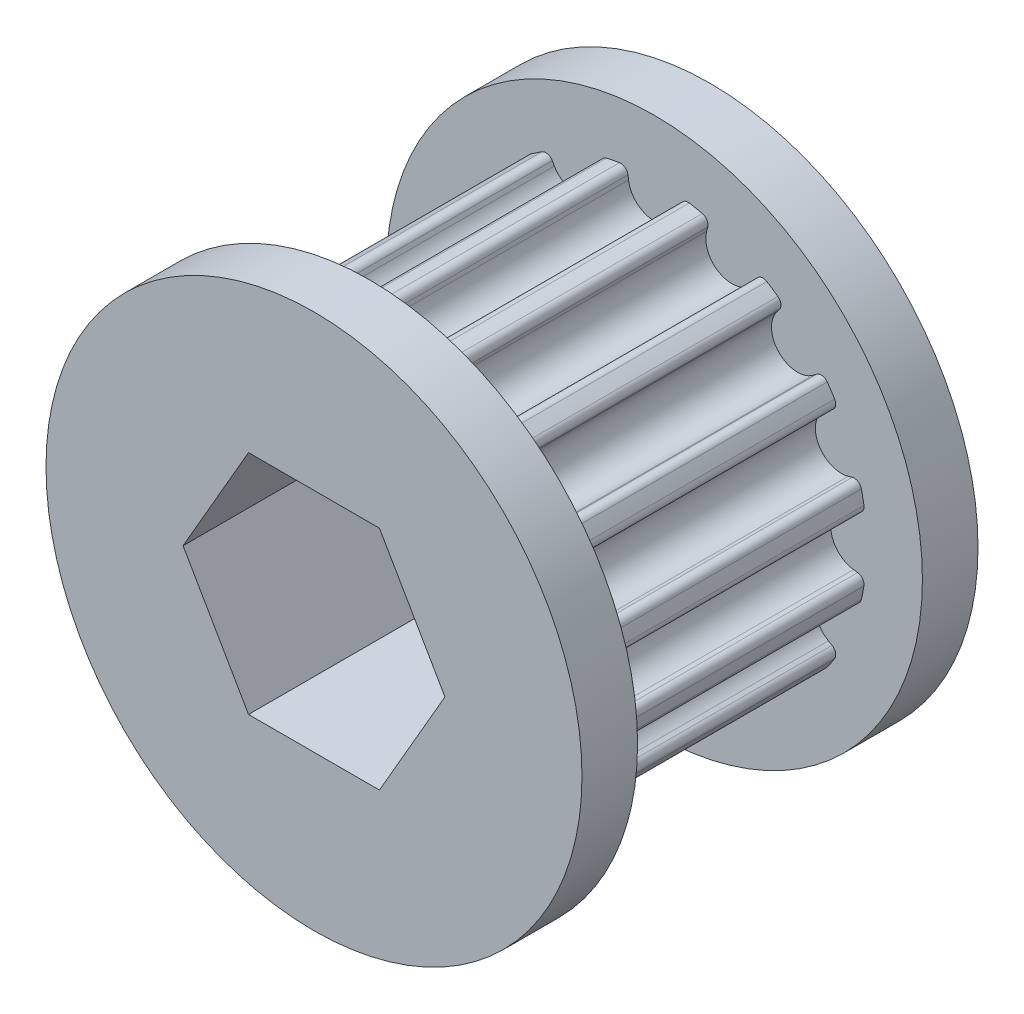
SolidWorks part; units mm, degrees
ref_plane "Front Plane" through (0, 0, 0) normal (0, 0, 1) x (1, 0, 0)
ref_plane "Top Plane" through (0, 0, 0) normal (0, 1, 0) x (1, 0, 0)
ref_plane "Right Plane" through (0, 0, 0) normal (1, 0, 0) x (0, 0, -1)
ref_plane "Plane1" through (0, 0, 0) normal (0, -1, 0) x (1, 0, 0)
sketch "Sketch1" plane through (0, 0, 0) normal (0, -1, 0) x (1, 0, 0)
  line L0 (15.3074, 3.175) -> (0, 3.175)
  line L1 (0, 3.175) -> (0, 0)
  line L2 (0, 0) -> (15.3074, 0)
  line L3 (15.3074, 0) -> (15.3074, 3.175)
  line L4 (0, 3.175) -> (0, 0) construction
revolve "Revolve1" add sketch "Sketch1" angle 360 about L4
sketch "Sketch2" plane through (0, 0, 3.175) normal (0, 0, 1) x (1, 0, 0)
  line L0 (1.5635, -12.0312) -> (1.4776, -11.3704)
  line L1 (-1.4776, -11.3704) -> (-1.5635, -12.0312)
  line L2 (-3.1597, -11.7137) -> (-2.9862, -11.0703)
  line L3 (-5.7164, -9.9394) -> (-6.0486, -10.5171)
  line L4 (-7.4018, -9.6129) -> (-6.9953, -9.0849)
  line L5 (-9.0849, -6.9953) -> (-9.6129, -7.4018)
  line L6 (-10.5171, -6.0486) -> (-9.9394, -5.7164)
  line L7 (-11.0703, -2.9862) -> (-11.7137, -3.1597)
  line L8 (-12.0312, -1.5635) -> (-11.3704, -1.4776)
  line L9 (-11.3704, 1.4776) -> (-12.0312, 1.5635)
  line L10 (-11.7137, 3.1597) -> (-11.0703, 2.9862)
  line L11 (-9.9394, 5.7164) -> (-10.5171, 6.0486)
  line L12 (-9.6129, 7.4018) -> (-9.0849, 6.9953)
  line L13 (-6.9953, 9.0849) -> (-7.4018, 9.6129)
  line L14 (-6.0486, 10.5171) -> (-5.7164, 9.9394)
  line L15 (-2.9862, 11.0703) -> (-3.1597, 11.7137)
  line L16 (-1.5635, 12.0312) -> (-1.4776, 11.3704)
  line L17 (1.4776, 11.3704) -> (1.5635, 12.0312)
  line L18 (3.1597, 11.7137) -> (2.9862, 11.0703)
  line L19 (5.7164, 9.9394) -> (6.0486, 10.5171)
  line L20 (7.4018, 9.6129) -> (6.9953, 9.0849)
  line L21 (9.0849, 6.9953) -> (9.6129, 7.4018)
  line L22 (10.5171, 6.0486) -> (9.9394, 5.7164)
  line L23 (11.0703, 2.9862) -> (11.7137, 3.1597)
  line L24 (12.0312, 1.5635) -> (11.3704, 1.4776)
  line L25 (11.3704, -1.4776) -> (12.0312, -1.5635)
  line L26 (11.7137, -3.1597) -> (11.0703, -2.9862)
  line L27 (9.9394, -5.7164) -> (10.5171, -6.0486)
  line L28 (9.6129, -7.4018) -> (9.0849, -6.9953)
  line L29 (6.9953, -9.0849) -> (7.4018, -9.6129)
  line L30 (6.0486, -10.5171) -> (5.7164, -9.9394)
  line L31 (2.9862, -11.0703) -> (3.1597, -11.7137)
  arc A0 (1.4776, -11.3704) -> (-1.4776, -11.3704) centre (0, -11.5624) ccw
  arc A1 (-1.5635, -12.0312) -> (-3.1597, -11.7137) centre (0, 0) cw
  arc A2 (-2.9862, -11.0703) -> (-5.7164, -9.9394) centre (-4.4247, -10.6823) ccw
  arc A3 (-6.0486, -10.5171) -> (-7.4018, -9.6129) centre (0, 0) cw
  arc A4 (-6.9953, -9.0849) -> (-9.0849, -6.9953) centre (-8.1758, -8.1758) ccw
  arc A5 (-9.6129, -7.4018) -> (-10.5171, -6.0486) centre (0, 0) cw
  arc A6 (-9.9394, -5.7164) -> (-11.0703, -2.9862) centre (-10.6823, -4.4247) ccw
  arc A7 (-11.7137, -3.1597) -> (-12.0312, -1.5635) centre (0, 0) cw
  arc A8 (-11.3704, -1.4776) -> (-11.3704, 1.4776) centre (-11.5624, 0) ccw
  arc A9 (-12.0312, 1.5635) -> (-11.7137, 3.1597) centre (0, 0) cw
  arc A10 (-11.0703, 2.9862) -> (-9.9394, 5.7164) centre (-10.6823, 4.4247) ccw
  arc A11 (-10.5171, 6.0486) -> (-9.6129, 7.4018) centre (0, 0) cw
  arc A12 (-9.0849, 6.9953) -> (-6.9953, 9.0849) centre (-8.1758, 8.1758) ccw
  arc A13 (-7.4018, 9.6129) -> (-6.0486, 10.5171) centre (0, 0) cw
  arc A14 (-5.7164, 9.9394) -> (-2.9862, 11.0703) centre (-4.4247, 10.6823) ccw
  arc A15 (-3.1597, 11.7137) -> (-1.5635, 12.0312) centre (0, 0) cw
  arc A16 (-1.4776, 11.3704) -> (1.4776, 11.3704) centre (0, 11.5624) ccw
  arc A17 (1.5635, 12.0312) -> (3.1597, 11.7137) centre (0, 0) cw
  arc A18 (2.9862, 11.0703) -> (5.7164, 9.9394) centre (4.4247, 10.6823) ccw
  arc A19 (6.0486, 10.5171) -> (7.4018, 9.6129) centre (0, 0) cw
  arc A20 (6.9953, 9.0849) -> (9.0849, 6.9953) centre (8.1758, 8.1758) ccw
  arc A21 (9.6129, 7.4018) -> (10.5171, 6.0486) centre (0, 0) cw
  arc A22 (9.9394, 5.7164) -> (11.0703, 2.9862) centre (10.6823, 4.4247) ccw
  arc A23 (11.7137, 3.1597) -> (12.0312, 1.5635) centre (0, 0) cw
  arc A24 (11.3704, 1.4776) -> (11.3704, -1.4776) centre (11.5624, 0) ccw
  arc A25 (12.0312, -1.5635) -> (11.7137, -3.1597) centre (0, 0) cw
  arc A26 (11.0703, -2.9862) -> (9.9394, -5.7164) centre (10.6823, -4.4247) ccw
  arc A27 (10.5171, -6.0486) -> (9.6129, -7.4018) centre (0, 0) cw
  arc A28 (9.0849, -6.9953) -> (6.9953, -9.0849) centre (8.1758, -8.1758) ccw
  arc A29 (7.4018, -9.6129) -> (6.0486, -10.5171) centre (0, 0) cw
  arc A30 (5.7164, -9.9394) -> (2.9862, -11.0703) centre (4.4247, -10.6823) ccw
  arc A31 (3.1597, -11.7137) -> (1.5635, -12.0312) centre (0, 0) cw
extrude "Boss-Extrude1" add sketch "Sketch2" along normal blind 16.27
ref_plane "Plane2" through (0, 0, 19.445) normal (0, 0, -1) x (-1, 0, 0)
sketch "Sketch3" plane through (0, 0, 19.445) normal (0, 0, -1) x (-1, 0, 0)
  circle A0 centre (0, 0) radius 15.3074
extrude "Boss-Extrude2" add sketch "Sketch3" against normal blind 3.175
sketch "Sketch4" plane through (0, 0, 22.62) normal (0, 0, 1) x (1, 0, 0)
  line L0 (-7.479, 0) -> (-3.7395, -6.477)
  line L1 (-3.7395, -6.477) -> (3.7395, -6.477)
  line L2 (3.7395, -6.477) -> (7.479, 0)
  line L3 (7.479, 0) -> (3.7395, 6.477)
  line L4 (3.7395, 6.477) -> (-3.7395, 6.477)
  line L5 (-3.7395, 6.477) -> (-7.479, 0)
extrude "Cut-Extrude1" cut sketch "Sketch4" against normal through all
fillet "Fillet1" radius 0.42 32 edges at (-1.5635, 12.0312, 11.31) (12.0312, -1.5635, 11.31) (7.4018, -9.6129, 11.31) (-3.1597, 11.7137, 11.31) (9.6129, 7.4018, 11.31) (-9.6129, 7.4018, 11.31) (3.1597, -11.7137, 11.31) (-7.4018, 9.6129, 11.31) (10.5171, -6.0486, 11.31) (-11.7137, 3.1597, 11.31) (11.7137, 3.1597, 11.31) (-10.5171, 6.0486, 11.31) (6.0486, 10.5171, 11.31) (-12.0312, -1.5635, 11.31) (6.0486, -10.5171, 11.31) (-12.0312, 1.5635, 11.31) (9.6129, -7.4018, 11.31) (-10.5171, -6.0486, 11.31) (11.7137, -3.1597, 11.31) (-11.7137, -3.1597, 11.31) (12.0312, 1.5635, 11.31) (-7.4018, -9.6129, 11.31) (10.5171, 6.0486, 11.31) (-9.6129, -7.4018, 11.31) (7.4018, 9.6129, 11.31) (-3.1597, -11.7137, 11.31) (3.1597, 11.7137, 11.31) (-6.0486, -10.5171, 11.31) (1.5635, 12.0312, 11.31) (1.5635, -12.0312, 11.31) (-6.0486, 10.5171, 11.31) (-1.5635, -12.0312, 11.31)
